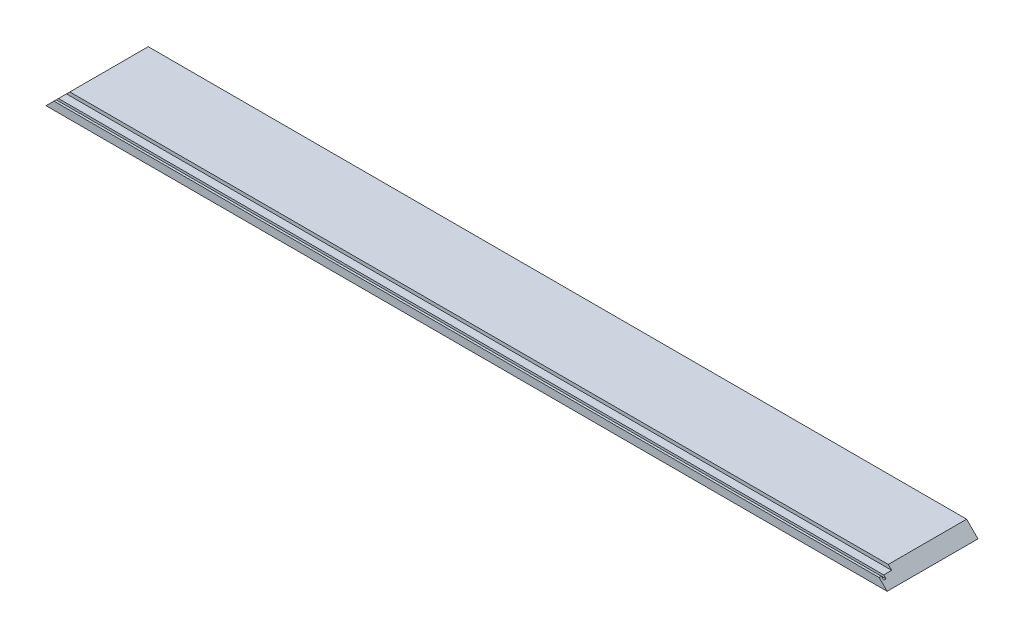
SolidWorks part; units mm, degrees
ref_plane "Front Plane" through (0, 0, 0) normal (0, 0, 1) x (1, 0, 0)
ref_plane "Top Plane" through (0, 0, 0) normal (0, 1, 0) x (1, 0, 0)
ref_plane "Right Plane" through (0, 0, 0) normal (1, 0, 0) x (0, 0, -1)
sketch "Sketch1" plane through (0, 0, 0) normal (0, 1, 0) x (1, 0, 0)
  line L1 (-370.25, 40) -> (370.25, 40)
  line L2 (-370.25, 40) -> (-370.25, -40)
  line L3 (-370.25, -40) -> (370.25, -40)
  line L4 (370.25, 40) -> (370.25, -40)
  line L5 (-370.25, 40) -> (370.25, -40) construction
  line L6 (-370.25, -40) -> (370.25, 40) construction
  point P0 (0, 0)
  dimension "D1" = 80
  dimension "D2" = 740.5
extrude "Boss-Extrude1" add sketch "Sketch1" along normal blind 10
sketch "Sketch2" plane through (-370.25, 0, 0) normal (-1, 0, 0) x (0, 0, 1)
  line L1 (40, 10) -> (29, 10)
  line L2 (40, 10) -> (40, 7)
  line L3 (40, 7) -> (29, 7)
  line L4 (29, 10) -> (29, 7)
  dimension "D1" = 3
  dimension "D2" = 11
extrude "Cut-Extrude1" cut sketch "Sketch2" against normal through all
sketch "Sketch3" plane through (-370.25, 0, 0) normal (-1, 0, 0) x (0, 0, 1)
  line L0 (29, 7) -> (40, 7) construction
  line L1 (38, 7) -> (36, 7)
  line L2 (38, 7) -> (38, 5)
  line L3 (38, 5) -> (36, 5)
  line L4 (36, 7) -> (36, 5)
  line L5 (40, 7) -> (40, 0) construction
  dimension "D1" = 2
  dimension "D2" = 2
  dimension "D3" = 2
extrude "Cut-Extrude2" cut sketch "Sketch3" against normal through all
sketch "Sketch4" plane through (0, 0, -40) normal (0, 0, -1) x (-1, 0, 0)
  line L0 (-370.25, 0) -> (-360.25, 10)
  line L2 (-360.25, 10) -> (-370.25, 10)
  line L3 (-370.25, 10) -> (-370.25, 0)
  line L4 (-370.25, 10) -> (370.25, 10) construction
  line L5 (0, 0) -> (0, 10) construction
  line L6 (-370.25, 0) -> (370.25, 0) construction
  line L7 (370.25, 10) -> (370.25, 0)
  line L8 (360.25, 10) -> (370.25, 10)
  line L9 (370.25, 0) -> (360.25, 10)
  dimension "D1" = 45
extrude "Cut-Extrude4" cut sketch "Sketch4" against normal through all
